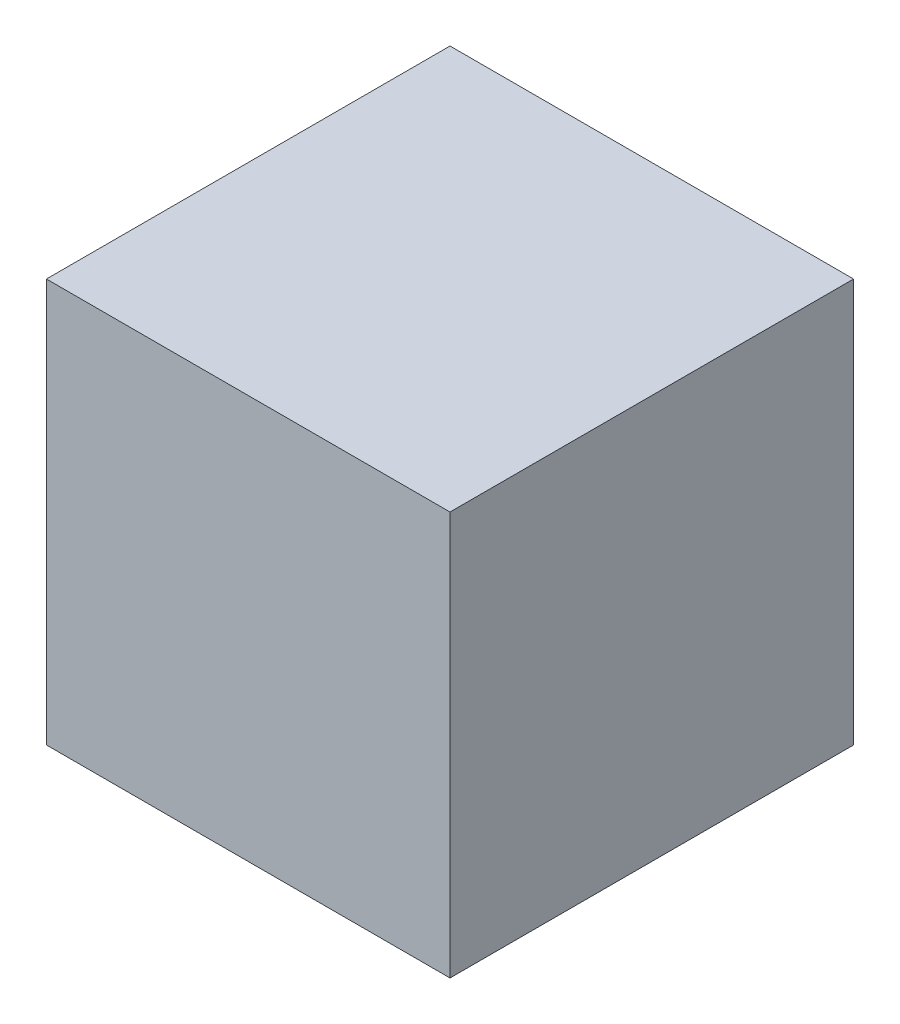
SolidWorks part; units mm, degrees
ref_plane "Front Plane" through (0, 0, 0) normal (0, 0, 1) x (1, 0, 0)
ref_plane "Top Plane" through (0, 0, 0) normal (0, 1, 0) x (1, 0, 0)
ref_plane "Right Plane" through (0, 0, 0) normal (1, 0, 0) x (0, 0, -1)
sketch "Sketch1" plane through (0, 0, 0) normal (0, 1, 0) x (1, 0, 0)
  line L1 (75, -75) -> (-75, -75)
  line L2 (75, -75) -> (75, 75)
  line L3 (75, 75) -> (-75, 75)
  line L4 (-75, -75) -> (-75, 75)
  line L5 (75, -75) -> (-75, 75) construction
  line L6 (75, 75) -> (-75, -75) construction
  point P0 (0, 0)
  dimension "D1" = 150
  dimension "D2" = 150
extrude "Boss-Extrude1" add sketch "Sketch1" along normal blind 150
